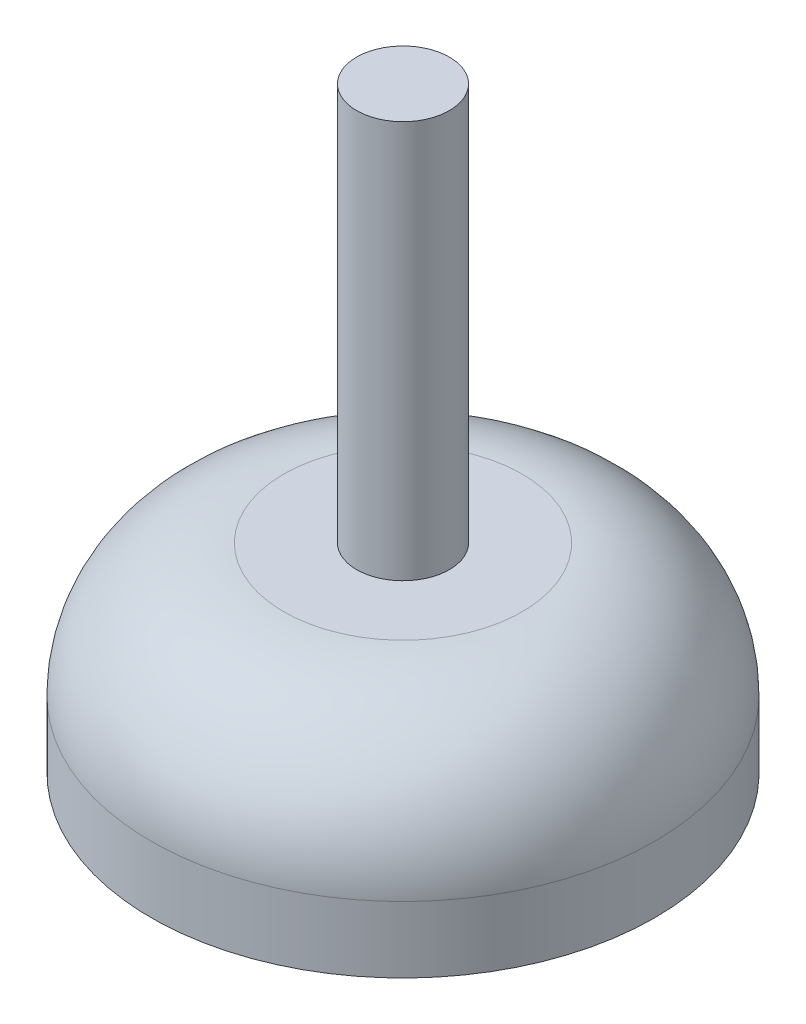
SolidWorks part; units mm, degrees
ref_plane "Plan de face" through (0, 0, 0) normal (0, 0, 1) x (1, 0, 0)
ref_plane "Plan de dessus" through (0, 0, 0) normal (0, 1, 0) x (1, 0, 0)
ref_plane "Plan de droite" through (0, 0, 0) normal (1, 0, 0) x (0, 0, -1)
sketch "Esquisse1" plane through (0, 0, 0) normal (0, 0, 1) x (1, 0, 0)
  line L0 (0, 0) -> (0, -45)
  line L1 (0, -45) -> (-19, -45)
  line L2 (-19, -45) -> (-19, -30)
  line L3 (-19, -30) -> (-3.5, -30)
  line L4 (-3.5, -30) -> (-3.5, 0)
  line L5 (-3.5, 0) -> (0, 0)
  dimension "D1" = 3.5
  dimension "D2" = 19
  dimension "D3" = 15
  dimension "D4" = 30
revolve "Révolution1" add sketch "Esquisse1" angle 360 about L0
fillet "Congé1" radius 10 1 edges at (-19, -30, 0)
